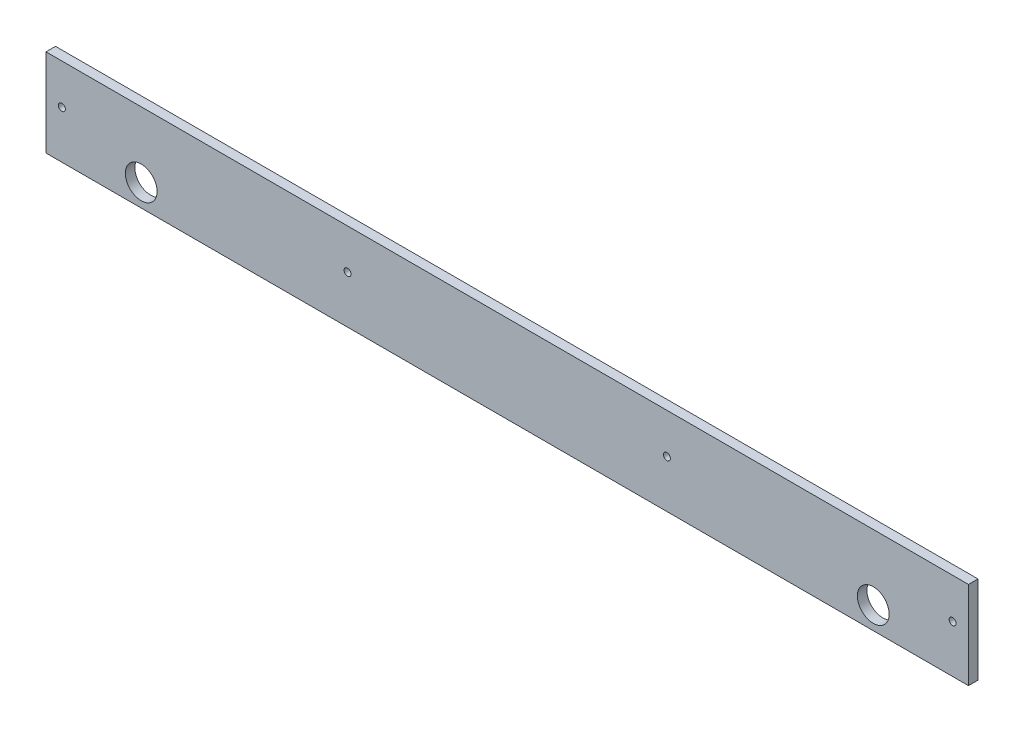
SolidWorks part; units mm, degrees
ref_plane "Plane1" through (0, 0, 0) normal (0, 0, 1) x (1, 0, 0)
ref_plane "Plane2" through (0, 0, 0) normal (0, 1, 0) x (1, 0, 0)
ref_plane "Plane3" through (0, 0, 0) normal (1, 0, 0) x (0, 0, -1)
sketch "Esquisse5" plane through (0, 0, 0) normal (0, 0, 1) x (1, 0, 0)
  line L5 (-3.927, 27.625) -> (286.6703, 27.625)
  line L6 (-3.927, 27.625) -> (-3.927, 0)
  line L7 (-3.927, 0) -> (286.6703, 0)
  line L8 (286.6703, 27.625) -> (286.6703, 0)
  circle A0 centre (281.6703, 15) radius 1.1
  circle A1 centre (91.073, 15) radius 1.1
  circle A2 centre (1.073, 15) radius 1.1
  circle A3 centre (191.6703, 15) radius 1.1
  dimension "D1" = 290.5973
  dimension "D3" = 2.2
  dimension "D2" = 27.625
  dimension "D4" = 5
  dimension "D5" = 90
  dimension "D6" = 5
  dimension "D7" = 90
  dimension "D8" = 15
  dimension "D9" = 3.927
extrude "Extrusion1" add sketch "Esquisse5" along normal blind 3
sketch "Esquisse4" plane through (0, 0, 3) normal (0, 0, 1) x (1, 0, 0)
  line L0 (-3.927, 0) -> (286.6703, 0) construction
  line L1 (-3.927, 27.625) -> (-3.927, 0) construction
  line L2 (286.6703, 0) -> (286.6703, 27.625) construction
  circle A0 centre (26.073, 7) radius 5
  circle A2 centre (256.6703, 7) radius 5
  dimension "D1" = 10
  dimension "D2" = 7
  dimension "D3" = 30
  dimension "D4" = 30
extrude "Enlèv. mat.-Extru.2" cut sketch "Esquisse4" against normal through all
